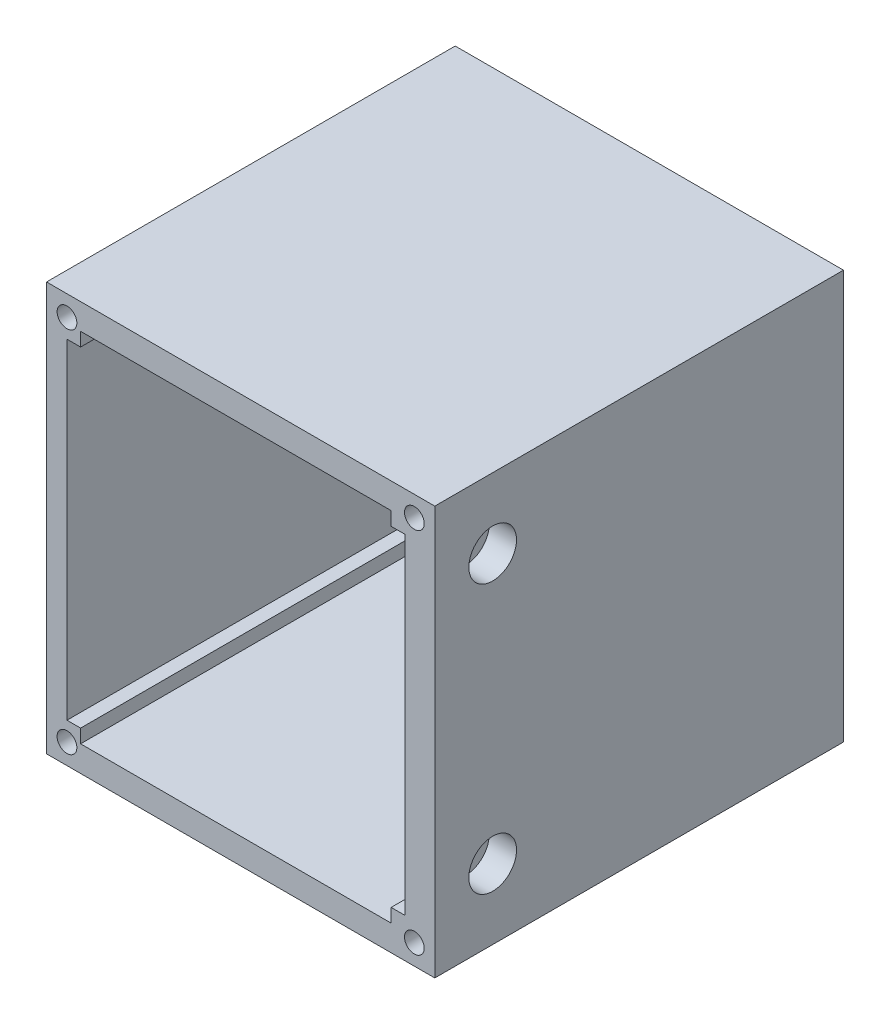
SolidWorks part; units mm, degrees
ref_plane "Front Plane" through (0, 0, 0) normal (0, 0, 1) x (1, 0, 0)
ref_plane "Top Plane" through (0, 0, 0) normal (0, 1, 0) x (1, 0, 0)
ref_plane "Right Plane" through (0, 0, 0) normal (1, 0, 0) x (0, 0, -1)
sketch "Sketch1" plane through (0, 0, 0) normal (0, 0, 1) x (1, 0, 0)
  line L146 (-17.5, 30) -> (-27.5, 30)
  line L147 (-17.5, -30) -> (17.5, -30)
  line L149 (-17.5, 30) -> (17.5, 30)
  line L150 (17.5, -30) -> (17.5, 30)
  line L151 (-27.5, 30) -> (-39.5, 30)
  line L152 (-39.5, 30) -> (-39.5, -30)
  line L154 (-27.5, -30) -> (-17.5, -30)
  line L155 (-39.5, -30) -> (-27.5, -30)
  point P0 (0, 0)
  dimension "D1" = 60
  dimension "D2" = 35
extrude "Boss-Extrude1" add sketch "Sketch1" along normal blind 60
sketch "Sketch3" plane through (0, 0, 60) normal (0, 0, 1) x (1, 0, 0)
  line L13 (-13.0954, -26.2247) -> (-23.1, -26.2247)
  line L17 (-13.0954, -26.2247) -> (11.0954, -26.2247)
  line L19 (-13.0954, 26.2247) -> (-23.1, 26.2247)
  line L21 (-13.0954, 26.2247) -> (11.0954, 26.2247)
  line L24 (-36.5, 26.2247) -> (-36.5, -26.2247)
  line L25 (13.0954, 0) -> (13.0954, 26.2247)
  line L26 (-23.1, 26.2247) -> (-36.5, 26.2247)
  line L27 (-23.1, -26.2247) -> (-36.5, -26.2247)
  line L28 (13.0954, 26.2247) -> (11.0954, 26.2247)
  line L29 (13.0954, 0) -> (13.0954, -26.2247)
  line L30 (13.0954, -26.2247) -> (11.0954, -26.2247)
  point P0 (0, 0)
extrude "Cut-Extrude1" cut sketch "Sketch3" against normal blind 56
sketch "Sketch6" plane through (0, 0, 0) normal (0, 0, -1) x (-1, 0, 0)
  line L1 (4, 15) -> (4, 19.2)
  line L2 (4, 15) -> (4, 10.8)
  line L6 (4, 19.2) -> (16, 19.2)
  line L7 (16, 19.2) -> (16, 10.8)
  line L8 (16, 10.8) -> (4, 10.8)
  line L16 (16, -10.8) -> (4, -10.8)
  line L17 (16, -19.2) -> (16, -10.8)
  line L18 (4, -19.2) -> (16, -19.2)
  line L19 (4, -15) -> (4, -10.8)
  line L20 (4, -15) -> (4, -19.2)
extrude "Cut-Extrude2" cut sketch "Sketch6" against normal through all
sketch "Sketch9" plane through (17.5, 0, 0) normal (1, 0, 0) x (0, 0, -1)
  circle A2 centre (-51.5, 19.7247) radius 3.5
  circle A3 centre (-51.5, -19.7247) radius 3.5
extrude "Cut-Extrude3" cut sketch "Sketch9" against normal blind 4
sketch "Sketch12" plane through (0, 0, 60) normal (0, 0, 1) x (1, 0, 0)
  line L0 (-36.5, 26.2247) -> (-34.5, 26.2247)
  line L1 (13.0954, -26.2247) -> (13.0954, -24.2247)
  line L2 (13.0954, 26.2247) -> (-36.5, 26.2247) construction
  line L3 (-34.5, 26.2247) -> (-34.5, 24.2247)
  line L4 (13.0954, -26.2247) -> (13.0954, 26.2247) construction
  line L5 (-34.5, 24.2247) -> (-36.5, 24.2247)
  line L6 (-36.5, 26.2247) -> (-36.5, -26.2247) construction
  line L7 (-36.5, 24.2247) -> (-36.5, 26.2247)
  line L8 (13.0954, 26.2247) -> (13.0954, 24.2247)
  line L9 (-36.5, -24.2247) -> (-36.5, -26.2247)
  line L10 (-34.5, -24.2247) -> (-36.5, -24.2247)
  line L11 (-34.5, -26.2247) -> (-34.5, -24.2247)
  line L12 (-36.5, -26.2247) -> (-34.5, -26.2247)
  line L13 (13.0954, -26.2247) -> (13.0954, 26.2247) construction
  line L14 (13.0954, 24.2247) -> (11.0954, 24.2247)
  line L15 (11.0954, 24.2247) -> (11.0954, 26.2247)
  line L16 (13.0954, 26.2247) -> (-36.5, 26.2247) construction
  line L17 (11.0954, 26.2247) -> (13.0954, 26.2247)
  line L18 (13.0954, -24.2247) -> (11.0954, -24.2247)
  line L23 (11.0954, -24.2247) -> (11.0954, -26.2247)
  line L24 (-36.5, -26.2247) -> (13.0954, -26.2247) construction
  line L25 (11.0954, -26.2247) -> (13.0954, -26.2247)
extrude "Boss-Extrude3" add sketch "Sketch12" against normal up to surface (56 mm away) up to face at (-10, 15, 4)
sketch "Sketch13" plane through (0, 0, 60) normal (0, 0, 1) x (1, 0, 0)
  circle A19 centre (-36.5, 27) radius 1.45
  circle A21 centre (-36.5, -27) radius 1.45
  circle A22 centre (14.5, 27) radius 1.45
  circle A23 centre (14.5, -27) radius 1.45
extrude "Cut-Extrude5" cut sketch "Sketch13" against normal blind 6
sketch "Sketch16" plane through (0, 0, 4) normal (0, 0, 1) x (1, 0, 0)
  circle A0 centre (2.5, 15) radius 1.95
  circle A1 centre (2.5, -15) radius 1.95
extrude "Cut-Extrude6" cut sketch "Sketch16" against normal up to surface (4 mm away) up to face at (-10, 15, 0)
sketch "Sketch17" plane through (17.5, 0, 0) normal (1, 0, 0) x (0, 0, -1)
  circle A0 centre (-51.5, 19.7247) radius 2
  circle A1 centre (-51.5, -19.7247) radius 2
extrude "Cut-Extrude7" cut sketch "Sketch17" against normal up to surface (4.4046 mm away) up to face at (13.0954, 0, 32)
